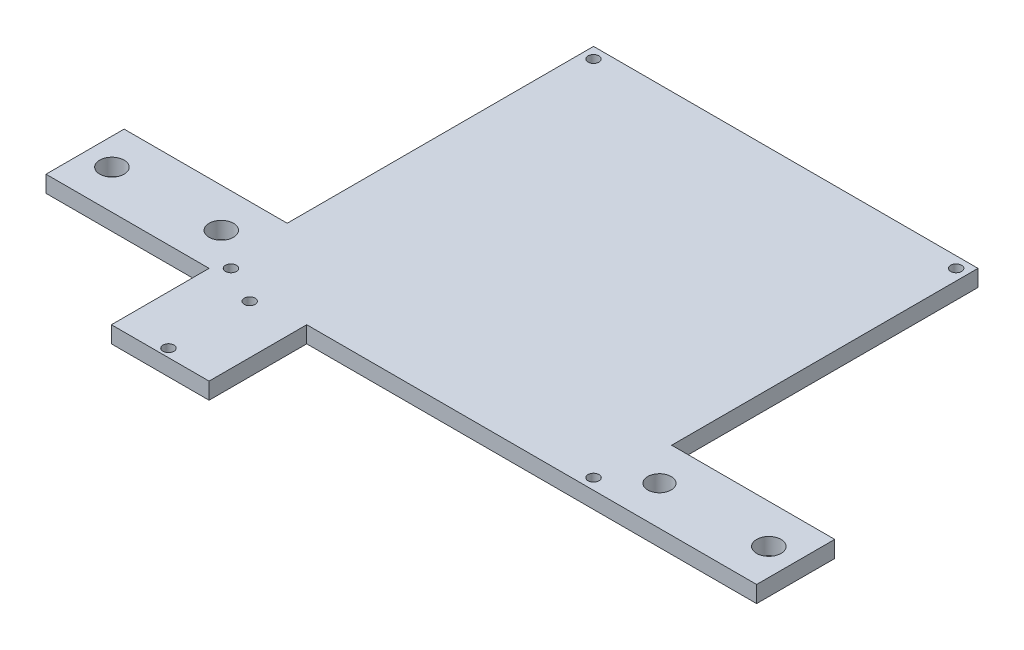
SolidWorks part; units mm, degrees
ref_plane "Front Plane" through (0, 0, 0) normal (0, 0, 1) x (1, 0, 0)
ref_plane "Top Plane" through (0, 0, 0) normal (0, 1, 0) x (1, 0, 0)
ref_plane "Right Plane" through (0, 0, 0) normal (1, 0, 0) x (0, 0, -1)
sketch "Sketch1" plane through (0, 0, 0) normal (0, 1, 0) x (1, 0, 0)
  line L0 (0, 20.32) -> (0, 100)
  line L1 (0, 100) -> (100, 100)
  line L2 (100, 100) -> (100, 20.32)
  line L5 (0, 0) -> (0, -25.4)
  line L6 (0, -25.4) -> (25.4, -25.4)
  line L7 (25.4, -25.4) -> (25.4, 0)
  line L8 (25.4, 0) -> (100, 0)
  line L9 (0, 0) -> (-42.418, 0)
  line L10 (-42.418, 0) -> (-42.418, 20.32)
  line L11 (-42.418, 20.32) -> (0, 20.32)
  line L12 (100, 0) -> (142.418, 0)
  line L13 (142.418, 0) -> (142.418, 20.32)
  line L14 (142.418, 20.32) -> (100, 20.32)
  circle A0 centre (2.8448, 2.8448) radius 1.4224
  circle A1 centre (97.1552, 2.8448) radius 1.4224
  circle A2 centre (2.8448, 97.1552) radius 1.4224
  circle A3 centre (97.1552, 97.1552) radius 1.4224
  circle A4 centre (12.7, -23.2664) radius 1.4224
  circle A5 centre (12.7, -2.1336) radius 1.4224
  circle A6 centre (-6.985, 10.16) radius 3.175
  circle A7 centre (-35.433, 10.16) radius 3.175
  circle A8 centre (106.985, 10.16) radius 3.048
  circle A9 centre (135.433, 10.16) radius 3.175
  point P34 (0, 0)
  dimension "D1" = 2.8448
  dimension "D2" = 6.985
  dimension "D3" = 6.985
  dimension "D5" = 2.8448
  dimension "D7" = 2.8448
  dimension "D9" = 2.8448
  dimension "D10" = 2.1336
  dimension "D17" = 10.16
  dimension "D4" = 2.8448
  dimension "D6" = 2.8448
  dimension "D8" = 2.8448
  dimension "D11" = 10.16
  dimension "D12" = 12.7
  dimension "D13" = 12.7
  dimension "D14" = 10.16
  dimension "D15" = 6.985
  dimension "D16" = 6.985
  dimension "D18" = 10.16
extrude "Boss-Extrude2" add sketch "Sketch1" along normal blind 4.318
